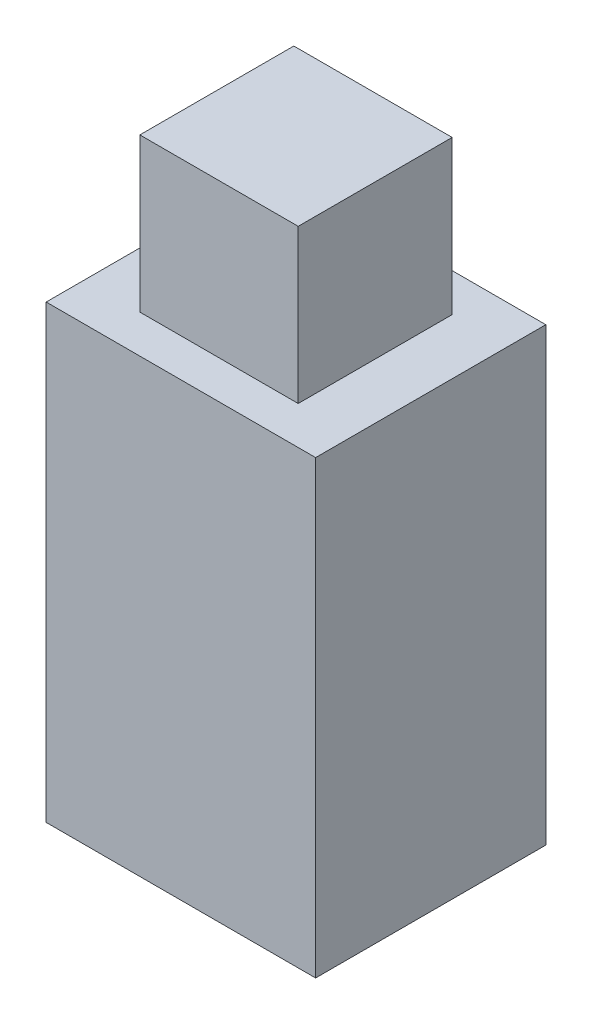
SolidWorks part; units mm, degrees
ref_plane "Front Plane" through (0, 0, 0) normal (0, 0, 1) x (1, 0, 0)
ref_plane "Top Plane" through (0, 0, 0) normal (0, 1, 0) x (1, 0, 0)
ref_plane "Right Plane" through (0, 0, 0) normal (1, 0, 0) x (0, 0, -1)
sketch "Sketch1" plane through (0, 0, 0) normal (0, 0, 1) x (1, 0, 0)
  line L1 (-51.5518, -71.8594) -> (18.6789, -71.8594)
  line L2 (-51.5518, -71.8594) -> (-51.5518, 45.6167)
  line L3 (-51.5518, 45.6167) -> (18.6789, 45.6167)
  line L4 (18.6789, -71.8594) -> (18.6789, 45.6167)
  line L5 (-51.5518, -71.8594) -> (18.6789, 45.6167) construction
  line L6 (-51.5518, 45.6167) -> (18.6789, -71.8594) construction
  point P0 (-16.4364, -13.1214)
extrude "Boss-Extrude1" add sketch "Sketch1" along normal blind 60
sketch "Sketch2" plane through (0, 45.6167, 0) normal (0, 1, 0) x (1, 0, 0)
  line L1 (4.2, -50.0657) -> (-37.0728, -50.0657)
  line L2 (4.2, -50.0657) -> (4.2, -9.9343)
  line L3 (4.2, -9.9343) -> (-37.0728, -9.9343)
  line L4 (-37.0728, -50.0657) -> (-37.0728, -9.9343)
  line L5 (4.2, -50.0657) -> (-37.0728, -9.9343) construction
  line L6 (4.2, -9.9343) -> (-37.0728, -50.0657) construction
  point P0 (-16.4364, -30)
extrude "Boss-Extrude2" add sketch "Sketch2" along normal blind 40
